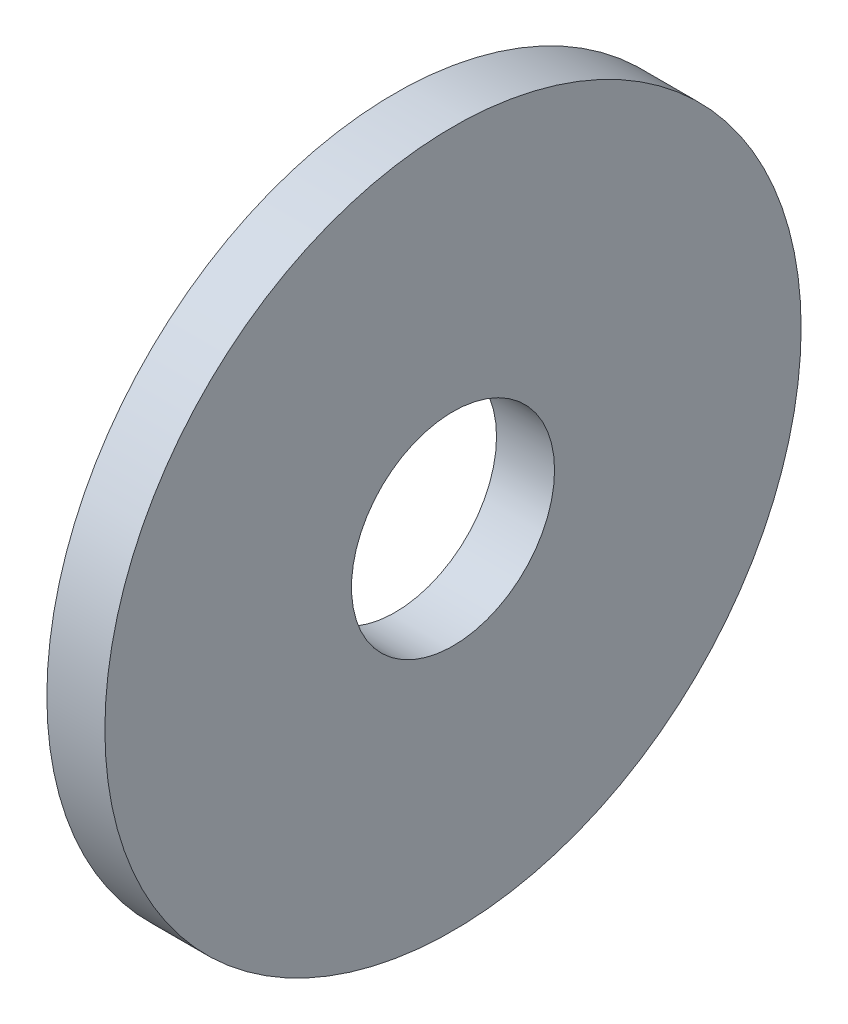
SolidWorks part; units mm, degrees
material "6063-O"
ref_plane "Front" through (0, 0, 0) normal (0, 0, 1) x (1, 0, 0)
ref_plane "Top" through (0, 0, 0) normal (0, 1, 0) x (1, 0, 0)
ref_plane "Right" through (0, 0, 0) normal (1, 0, 0) x (0, 0, -1)
sketch "草图1" plane through (0, 0, 0) normal (1, 0, 0) x (0, 0, -1)
  circle A0 centre (0, 0) radius 1.75
  circle A1 centre (0, 0) radius 6
  dimension "D1" = 3.5
  dimension "D2" = 12
extrude "凸台-拉伸1" add sketch "草图1" along normal blind 1
